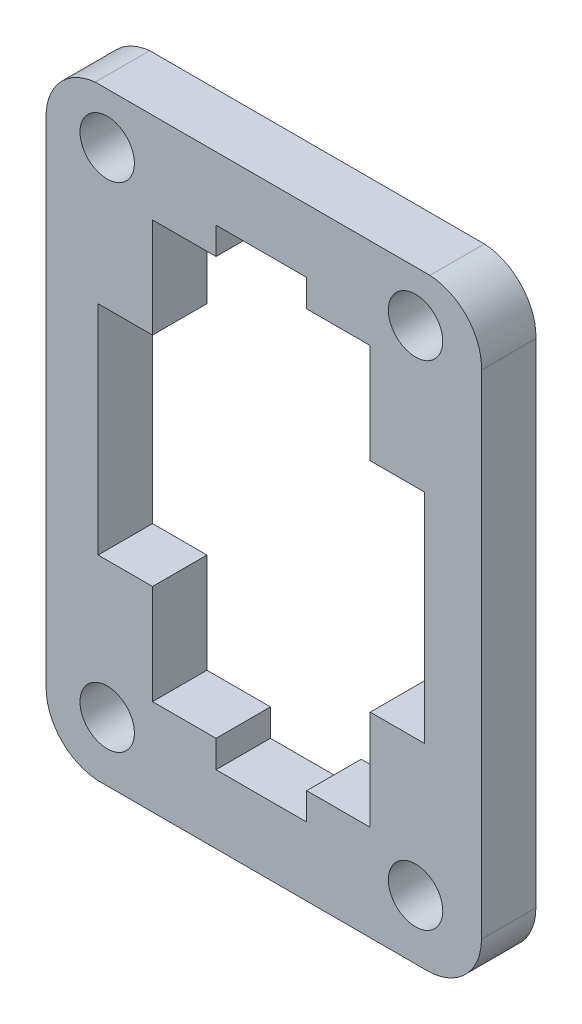
SolidWorks part; units mm, degrees
ref_plane "Front Plane" through (0, 0, 0) normal (0, 0, 1) x (1, 0, 0)
ref_plane "Top Plane" through (0, 0, 0) normal (0, 1, 0) x (1, 0, 0)
ref_plane "Right Plane" through (0, 0, 0) normal (1, 0, 0) x (0, 0, -1)
sketch "Model" plane through (0, 0, 0) normal (0, 0, 1) x (1, 0, 0)
  line L0 (50.4999, 54) -> (55.4999, 54)
  line L1 (55.4999, 52.5) -> (58.9999, 52.5)
  line L2 (58.9999, 47) -> (61.9999, 47)
  line L3 (61.9999, 35) -> (58.9999, 35)
  line L4 (58.9999, 29.5) -> (55.4999, 29.5)
  line L5 (55.4999, 28.0001) -> (50.4999, 28.0001)
  line L6 (50.4999, 29.5) -> (46.9999, 29.5)
  line L7 (46.9999, 35) -> (44.0001, 35)
  line L8 (44.0001, 47) -> (46.9999, 47)
  line L9 (46.9999, 52.5) -> (50.4999, 52.5)
  line L10 (50.4999, 54) -> (50.4999, 52.5)
  line L11 (46.9999, 52.5) -> (46.9999, 47)
  line L12 (44.0001, 47) -> (44.0001, 35)
  line L13 (46.9999, 35) -> (46.9999, 29.5)
  line L14 (50.4999, 29.5) -> (50.4999, 28.0001)
  line L15 (55.4999, 28.0001) -> (55.4999, 29.5)
  line L16 (58.9999, 29.5) -> (58.9999, 35)
  line L17 (61.9999, 35) -> (61.9999, 47)
  line L18 (58.9999, 47) -> (58.9999, 52.5)
  line L19 (55.4999, 52.5) -> (55.4999, 54)
  line L20 (41.1334, 44.2121) -> (41.1334, 27.226)
  line L21 (43.843, 57.5) -> (47.3465, 57.5)
  line L22 (44.1334, 24.226) -> (62.1332, 24.226)
  line L23 (59.3464, 57.5) -> (47.3465, 57.5)
  line L24 (65.1332, 44.226) -> (65.1332, 27.226)
  line L25 (65.1332, 44.226) -> (65.1332, 54.3972)
  line L26 (41.1334, 54.3832) -> (41.1334, 44.2121)
  line L27 (59.3464, 57.5) -> (62.2923, 57.5)
  circle A0 centre (44.4998, 54.7001) radius 1.5001
  circle A1 centre (61.4999, 54.7001) radius 1.5
  circle A2 centre (44.4999, 27.5) radius 1.5
  circle A3 centre (61.4999, 27.5) radius 1.5
  arc A4 (62.1332, 24.226) -> (65.1332, 27.226) centre (62.133, 27.2263) ccw
  arc A5 (65.1332, 54.3972) -> (62.2923, 57.5) centre (62.1352, 54.5042) ccw
  arc A6 (43.843, 57.5) -> (41.1334, 54.3832) centre (44.1304, 54.5139) ccw
  spline S0 degree 3 poles (41.1334, 27.226) (41.1334, 26.4304) (41.4494, 25.6674) (42.012, 25.1048) knots 0 0 0 0 0.333333 0.333333 0.333333 0.333333
  spline S1 degree 3 poles (42.012, 25.1048) (42.5746, 24.5422) (43.3377, 24.226) (44.1334, 24.226) knots 0.333333 0.333333 0.333333 0.333333 1 1 1 1
extrude "Boss-Extrude1" add sketch "Model" along normal blind 3
